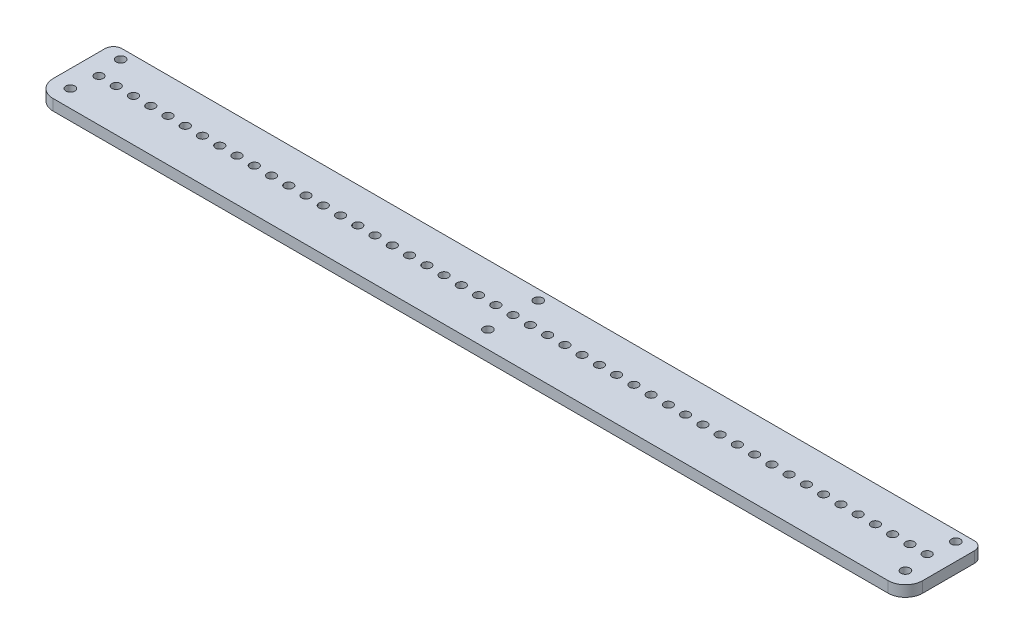
SolidWorks part; units mm, degrees
ref_plane "Front Plane" through (0, 0, 0) normal (0, 0, 1) x (1, 0, 0)
ref_plane "Top Plane" through (0, 0, 0) normal (0, 1, 0) x (1, 0, 0)
ref_plane "Right Plane" through (0, 0, 0) normal (1, 0, 0) x (0, 0, -1)
sketch "Sketch1" plane through (0, 0, 0) normal (0, 1, 0) x (1, 0, 0)
  line L1 (10, 0) -> (494, 0)
  line L2 (0, 10) -> (0, 40)
  line L3 (5, 45) -> (499, 45)
  line L4 (504, 10) -> (504, 40)
  line L5 (0, 0) -> (504, 45) construction
  line L6 (0, 45) -> (504, 0) construction
  arc A2 (504, 40) -> (499, 45) centre (499, 40) ccw
  arc A3 (5, 45) -> (0, 40) centre (5, 40) ccw
  arc A4 (504, 10) -> (494, 0) centre (494, 10) cw
  arc A5 (0, 10) -> (10, 0) centre (10, 10) ccw
  point P4 (252, 22.5)
  dimension "D3" = 5
  dimension "D4" = 10
  dimension "D1" = 45
  dimension "D2" = 504
extrude "Boss-Extrude1" add sketch "Sketch1" along normal blind 6.35
sketch "Sketch2" plane through (0, 6.35, 0) normal (0, 1, 0) x (1, 0, 0)
  line L0 (504, 10) -> (504, 40) construction
  line L1 (10, 0) -> (494, 0) construction
  point P0 (492, 24.6)
  dimension "D1" = 12
  dimension "D2" = 24.6
hole_wizard "M6x1.0 Tapped Hole1" positions "Sketch3" profile "Sketch4" tap size "M6x1.0" standard "Autoliv NAM Metric" end condition through all
sketch "Sketch3" plane through (0, 6.35, 0) normal (0, 1, 0) x (1, 0, 0)
  point P0 (492, 24.6)
sketch "Sketch4" plane through (492, 6.35, -24.6) normal (1, 0, 0) x (0, 0, 1)
  line L0 (0, 0) -> (0, 6.35)
  line L1 (0, 6.35) -> (2.5, 6.35)
  line L2 (2.5, 6.35) -> (2.5, 0)
  line L5 (2.5, 0) -> (0, 0)
  line L11 (0, -6.35) -> (0, 107.95) construction
  dimension "Thru Tap Drill Dia." = 5
  dimension "Thru Tap Drill Depth" = 6.35
cosmetic thread "Hole Thread1" parameters "D2"=6
pattern_linear "LPattern1" count 49 spacing 10 along (-1, 0, 0) of "M6x1.0 Tapped Hole1"
sketch "Sketch5" plane through (0, 6.35, 0) normal (0, 1, 0) x (1, 0, 0)
  line L2 (252, 0) -> (252, 45) construction
  line L3 (10, 0) -> (494, 0) construction
  line L4 (499, 45) -> (5, 45) construction
  circle A0 centre (10, 10) radius 2.6
  circle A1 centre (10, 39.2) radius 2.6
  circle A2 centre (494, 10) radius 2.6
  circle A3 centre (494, 39.2) radius 2.6
  circle A4 centre (252, 10) radius 2.6
  circle A5 centre (252, 39.2) radius 2.6
  arc A6 (0, 10) -> (10, 0) centre (10, 10) ccw construction
  arc A7 (494, 0) -> (504, 10) centre (494, 10) ccw construction
  dimension "D2" = 5.2
  dimension "D1" = 14.6
extrude "Cut-Extrude1" cut sketch "Sketch5" against normal up to next
